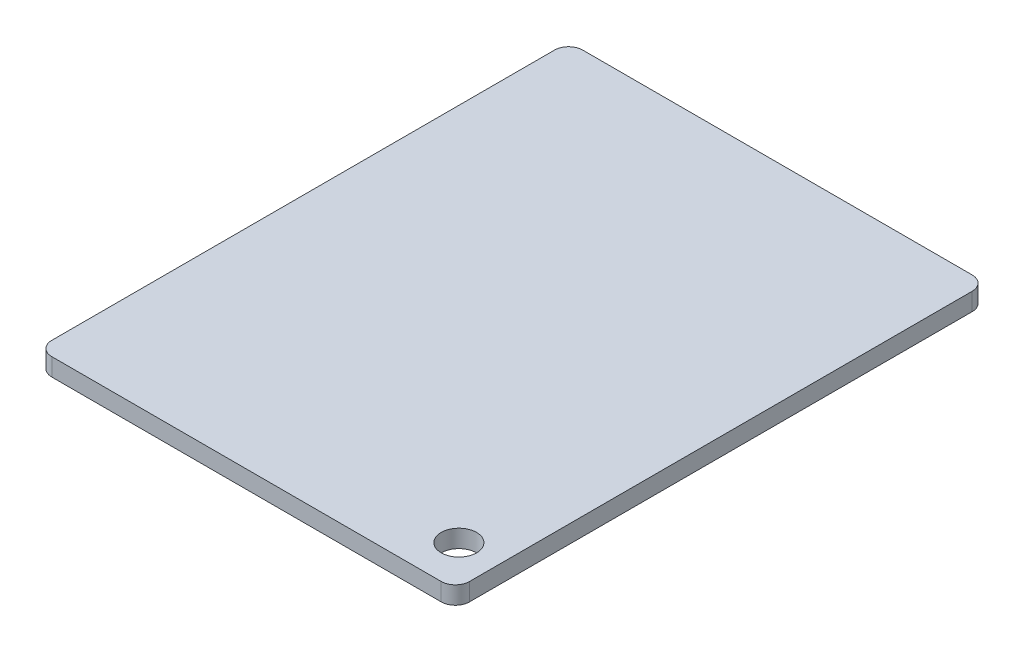
SolidWorks part; units mm, degrees
ref_plane "Front Plane" through (0, 0, 0) normal (0, 0, 1) x (1, 0, 0)
ref_plane "Top Plane" through (0, 0, 0) normal (0, 1, 0) x (1, 0, 0)
ref_plane "Right Plane" through (0, 0, 0) normal (1, 0, 0) x (0, 0, -1)
sketch "Sketch1" plane through (0, 0, 0) normal (0, 1, 0) x (1, 0, 0)
  line L0 (0, 0) -> (50.0616, 0) construction
  line L1 (-27.5, 35.5) -> (27.5, 35.5)
  line L2 (-27.5, 35.5) -> (-27.5, -35.5)
  line L3 (-27.5, -35.5) -> (27.5, -35.5)
  line L4 (27.5, 35.5) -> (27.5, -35.5)
  line L5 (0, 0) -> (0, -43.9772) construction
  line L6 (-27.5, 37.5) -> (27.5, 37.5)
  line L7 (29.5, 35.5) -> (29.5, -35.5)
  line L8 (-27.5, -37.5) -> (27.5, -37.5)
  line L9 (-29.5, 35.5) -> (-29.5, -35.5)
  arc A0 (29.5, -35.5) -> (27.5, -37.5) centre (27.5, -35.5) cw
  arc A1 (-27.5, -37.5) -> (-29.5, -35.5) centre (-27.5, -35.5) cw
  arc A2 (27.5, 37.5) -> (29.5, 35.5) centre (27.5, 35.5) cw
  arc A3 (-27.5, 37.5) -> (-29.5, 35.5) centre (-27.5, 35.5) ccw
  dimension "D3" = 2
  dimension "D4" = 2
  dimension "D5" = 2
  dimension "D6" = 2
  dimension "D1" = 55
  dimension "D2" = 71
  dimension "D7" = 2
  dimension "D8" = 2
  dimension "D9" = 2
  dimension "D10" = 2
extrude "Boss-Extrude1" add sketch "Sketch1" along normal blind 2.5 contours L4 L1 L2 L3 | L6 A3 L9 A1 L8 A0 L7 A2 L1 L4 L3 L2
sketch "Sketch2" plane through (0, 0, 0) normal (0, -1, 0) x (1, 0, 0)
  line L0 (26.5, 31.5) -> (26.5, 43.2988) construction
  line L1 (27.5, -35.5) -> (27.5, 35.5) construction
  line L2 (24, 34) -> (65.0764, 34) construction
  line L3 (-27.5, 35.5) -> (27.5, 35.5) construction
  circle A0 centre (24, 31.5) radius 2.5
  dimension "D1" = 5
  dimension "D2" = 1
  dimension "D3" = 1.5
extrude "Cut-Extrude1" cut sketch "Sketch2" against normal blind 22
sketch "Sketch3" plane through (0, 0, 0) normal (0, -1, 0) x (1, 0, 0)
  line L0 (26.4337, 26.6638) -> (26.4337, 3.6859) construction
  line L1 (-1.9641, 17.9979) -> (-1.9641, -22.0795) construction
  line L3 (6.8401, 13.1843) -> (6.8401, -14.2666) construction
  text T0 "<b>R E S E T</b>" font "Century Gothic" height 3.5
  text T1 "<b>POWERED BY </b>" font "Century Gothic" height 3.5
  text T2 "<b>ARDUINO</b>" font "Century Gothic" height 3.5
  point P6 (26.4337, 3.6859)
  point P7 (0, 0)
  point P8 (-3.0844, -1.2802)
  point P9 (-7.5188, 24.7982)
  point P10 (-7.3077, -2.5472)
  point P11 (-7.73, -24.1911)
  point P12 (-7.4132, 17.9354)
  point P15 (6.5234, -10.6769)
  point P16 (6.4178, 13.1843)
  point P17 (6.8401, -14.2666)
  point P18 (-4.7737, -22.0795)
  point P19 (0, 0)
  point P20 (-1.8462, 20.9448)
  point P21 (-1.9641, 17.9979)
extrude "Boss-Extrude2" add sketch "Sketch3" along normal blind 1
